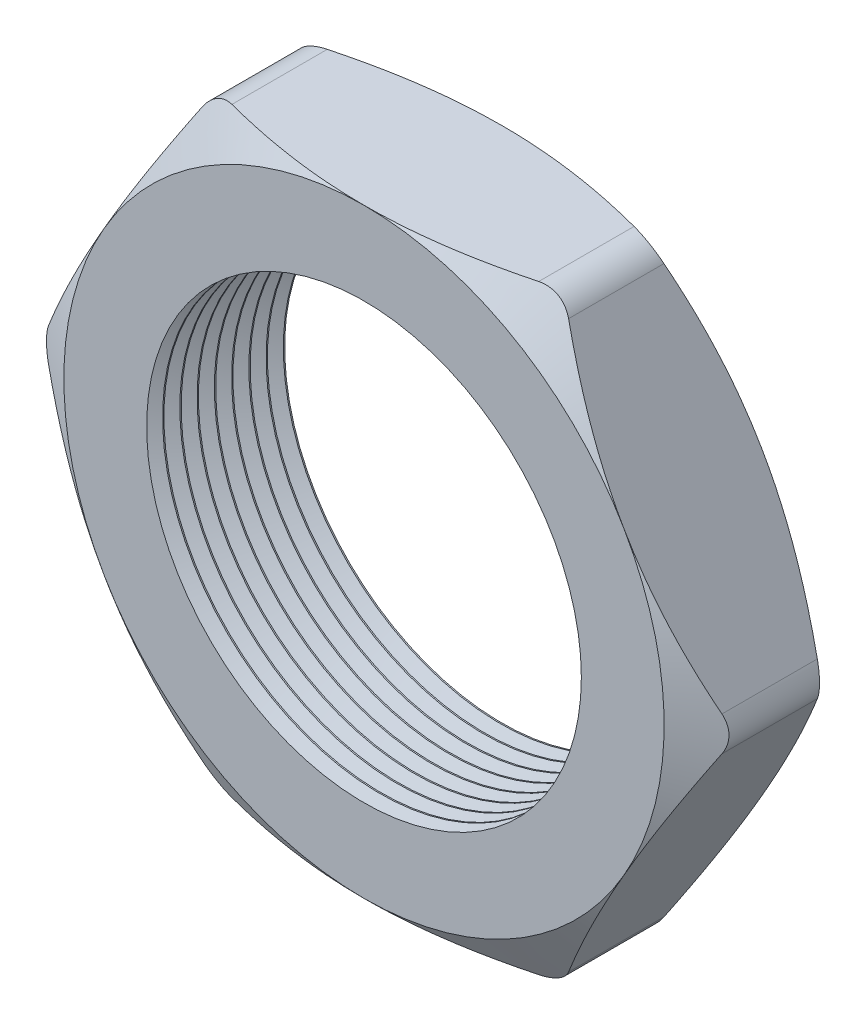
SolidWorks part; units mm, degrees
ref_plane "Front Plane" through (0, 0, 0) normal (0, 0, 1) x (1, 0, 0)
ref_plane "Top Plane" through (0, 0, 0) normal (0, 1, 0) x (1, 0, 0)
ref_plane "Right Plane" through (0, 0, 0) normal (1, 0, 0) x (0, 0, -1)
sketch "Sketch1" plane through (0, 0, 0) normal (0, 0, 1) x (1, 0, 0)
  line L1 (-12.7583, 0) -> (-6.3791, -11.049)
  line L2 (-6.3791, -11.049) -> (6.3791, -11.049)
  line L3 (6.3791, -11.049) -> (12.7583, 0)
  line L4 (12.7583, 0) -> (6.3791, 11.049)
  line L5 (6.3791, 11.049) -> (-6.3791, 11.049)
  line L6 (-6.3791, 11.049) -> (-12.7583, 0)
  circle A0 centre (0, 0) radius 11.049 construction
  circle A1 centre (0, 0) radius 8.001
  dimension "TS" = 16.002
  dimension "H" = 22.098
extrude "Extrude1" add sketch "Sketch1" along normal blind 5.08
sketch "Sketch2" plane through (0, 0, 5.08) normal (0, 0, 1) x (1, 0, 0)
  line L0 (6.3791, 11.049) -> (-6.3791, 11.049) construction
  circle A0 centre (0, 0) radius 11.049
extrude "Cut-Extrude1" cut sketch "Sketch2" against normal through all draft 60 flip side to cut
sketch "Sketch3" plane through (0, 0, 0) normal (0, 0, -1) x (-1, 0, 0)
  line L0 (-6.3791, 11.049) -> (6.3791, 11.049) construction
  circle A0 centre (0, 0) radius 11.049
extrude "Cut-Extrude2" cut sketch "Sketch3" against normal through all draft 60 flip side to cut
fillet "Fillet1" radius 1.27 6 edges at (12.7583, 0, 2.54) (6.3791, -11.049, 2.54) (-6.3791, -11.049, 2.54) (-12.7583, 0, 2.54) (-6.3791, 11.049, 2.54) (6.3791, 11.049, 2.54)
sketch "Sketch4" plane through (0, 0, 0) normal (0, 1, 0) x (1, 0, 0)
  line L0 (-8.001, -5.08) -> (-8.001, -4.4934)
  line L1 (-8.001, 0) -> (-8.001, -5.08) construction
  line L2 (-8.001, -4.4934) -> (-8.509, -4.7867)
  line L3 (-8.509, -4.7867) -> (-8.001, -5.08)
  dimension "D1" = 60
  dimension "D2" = 60
  dimension "D3" = 0.508
revolve "Cut-Revolve1" cut sketch "Sketch4" angle 360 about axis through (0, 0, 0) along (0, 0, 1)
pattern_linear "LPattern1" count 8 spacing 0.635 along (0, 0, -1) of "Cut-Revolve1"
